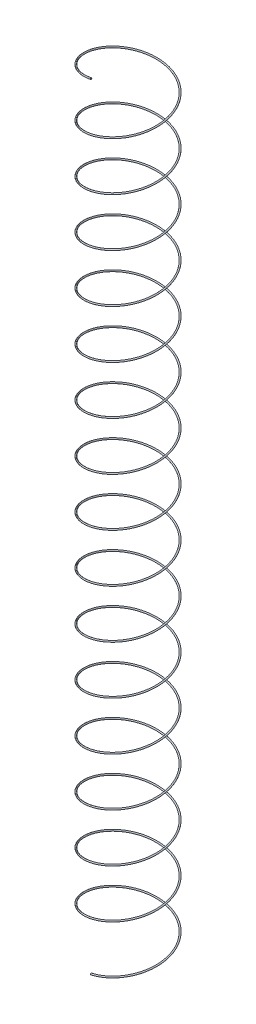
SolidWorks part; units mm, degrees
ref_plane "Front Plane" through (0, 0, 0) normal (0, 0, 1) x (1, 0, 0)
ref_plane "Top Plane" through (0, 0, 0) normal (0, 1, 0) x (1, 0, 0)
ref_plane "Right Plane" through (0, 0, 0) normal (1, 0, 0) x (0, 0, -1)
sketch "Center Axis" plane through (0, 0, 0) normal (1, 0, 0) x (0, 0, -1)
  line L0 (0, 0) -> (0, 49.506) construction
sketch "Diameter Stowed" plane through (0, 0, 0) normal (0, 1, 0) x (1, 0, 0)
  circle A0 centre (0, 0) radius 22.495
  dimension "D1" = 44.99
sketch "Diameter Deployed" plane through (0, 0, 0) normal (0, 1, 0) x (1, 0, 0)
  circle A0 centre (0, 0) radius 21.75
  dimension "D1" = 43.5
sketch "Wire Gauge XZ" plane through (0, 0, 0) normal (0, 1, 0) x (1, 0, 0)
  circle A0 centre (0, 0) radius 0.405
  dimension "D1" = 0.81
sketch "Wire Gauge YZ" plane through (0, 0, 0) normal (1, 0, 0) x (0, 0, -1)
  line L0 (0.405, 0) -> (-0.405, 0) construction
  line L1 (0, 0) -> (-0.405, 0) construction
  circle A0 centre (0, 0) radius 0.405
curve "Deployed Helix" pitch 28.6 height 457.6 turns 16
sketch "Sketch7" plane through (0, 0, 0) normal (1, 0, 0) x (0, 0, -1)
  circle A0 centre (-21.75, 0) radius 0.405
  circle A1 centre (0, 0) radius 0.405 construction
  spline S0 degree 3 poles (-21.75, 0) (-21.75, 0.4564) (-21.0842, 1.3749) (-18.1784, 2.7481) (-13.6284, 4.1226) (-7.8457, 5.4967) (-1.3533, 6.8709) (5.2614, 8.245) (11.4003, 9.6192) (16.508, 10.9934) (20.1226, 12.3676) (21.917, 13.7417) (21.7291, 15.1159) (19.5757, 16.4901) (15.6518, 17.8643) (10.3121, 19.2384) (4.0397, 20.6126) (-2.5982, 21.9868) (-9.001, 23.361) (-14.5896, 24.7351) (-18.8586, 26.1093) (-21.4219, 27.4835) (-22.0475, 28.8577) (-20.679, 30.2318) (-17.44, 31.606) (-12.6235, 32.9802) (-6.6653, 34.3544) (-0.1042, 35.7285) (6.4664, 37.1027) (12.452, 38.4769) (17.3114, 39.8511) (20.6049, 41.2252) (22.0348, 42.5994) (21.4715, 43.9736) (18.9662, 45.3477) (14.7454, 46.7219) (9.1908, 48.0961) (2.8049, 49.4703) (-3.8347, 50.8444) (-10.1274, 52.2186) (-15.5041, 53.5928) (-19.4784, 54.967) (-21.691, 56.3411) (-21.9415, 57.7153) (-20.2075, 59.0895) (-16.6457, 60.4637) (-11.5782, 61.8378) (-5.4635, 63.212) (1.1453, 64.5862) (7.6506, 65.9604) (13.4639, 67.3345) (18.0593, 68.7087) (21.0213, 70.0829) (22.0819, 71.4571) (21.1452, 72.8312) (18.2959, 74.2054) (13.7917, 75.5796) (8.0401, 76.9538) (1.5612, 78.3279) (-5.0589, 79.7021) (-11.2214, 81.0763) (-16.3689, 82.4505) (-20.0359, 83.8246) (-21.8906, 85.1988) (-21.7653, 86.573) (-19.6713, 87.9471) (-15.798, 89.3213) (-10.4958, 90.6955) (-4.2443, 92.0697) (2.3912, 93.4438) (8.8103, 94.818) (14.4326, 96.1922) (18.7494, 97.5664) (21.3704, 98.9405) (22.0583, 100.3147) (20.7511, 101.6889) (17.567, 103.0631) (12.7939, 104.4372) (6.8636, 105.8114) (0.3125, 107.1856) (-6.2669, 108.5598) (-12.2794, 109.9339) (-17.1813, 111.3081) (-20.5291, 112.6823) (-22.02, 114.0565) (-21.5193, 115.4306) (-19.0721, 116.8048) (-14.8998, 118.179) (-9.3798, 119.5532) (-3.0114, 120.9273) (3.6293, 122.3015) (9.9418, 123.6757) (15.3551, 125.0498) (19.3794, 126.424) (21.6509, 127.7982) (21.9641, 129.1724) (20.2906, 130.5465) (16.7818, 131.9207) (11.7551, 133.2949) (5.6652, 134.6691) (-0.9372, 136.0432) (-7.4548, 137.4174) (-13.2981, 138.7916) (-17.9386, 140.1658) (-20.9566, 141.5399) (-22.079, 142.9141) (-21.2043, 144.2883) (-18.4117, 145.6625) (-13.9538, 147.0366) (-8.2338, 148.4108) (-1.7689, 149.785) (4.8559, 151.1592) (11.0415, 152.5333) (16.2283, 153.9075) (19.9474, 155.2817) (21.8622, 156.6559) (21.7995, 158.03) (19.7651, 159.4042) (15.9429, 160.7784) (10.6787, 162.1526) (4.4485, 163.5267) (-2.1839, 164.9009) (-8.6189, 166.2751) (-14.2743, 167.6492) (-18.6385, 169.0234) (-21.3169, 170.3976) (-22.0672, 171.7718) (-20.8215, 173.1459) (-17.6925, 174.5201) (-12.9631, 175.8943) (-7.0613, 177.2685) (-0.5208, 178.6426) (6.0668, 180.0168) (12.1057, 181.391) (17.0496, 182.7652) (20.4514, 184.1393) (22.0033, 185.5135) (21.5651, 186.8877) (19.1762, 188.2619) (15.0529, 189.636) (9.568, 191.0102) (3.2177, 192.3844) (-3.4237, 193.7586) (-9.7553, 195.1327) (-15.2046, 196.5069) (-19.2787, 197.8811) (-21.609, 199.2553) (-21.9847, 200.6294) (-20.3719, 202.0036) (-16.9165, 203.3778) (-11.931, 204.752) (-5.8663, 206.1261) (0.729, 207.5003) (7.2584, 208.8745) (13.1312, 210.2486) (17.8163, 211.6228) (20.8899, 212.997) (22.0741, 214.3712) (21.2616, 215.7453) (18.526, 217.1195) (14.1147, 218.4937) (8.4267, 219.8679) (1.9765, 221.242) (-4.6524, 222.6162) (-10.8605, 223.9904) (-16.0863, 225.3646) (-19.8571, 226.7387) (-21.8318, 228.1129) (-21.8318, 229.4871) (-19.8571, 230.8613) (-16.0863, 232.2354) (-10.8605, 233.6096) (-4.6524, 234.9838) (1.9765, 236.358) (8.4267, 237.7321) (14.1147, 239.1063) (18.526, 240.4805) (21.2616, 241.8547) (22.0741, 243.2288) (20.8899, 244.603) (17.8163, 245.9772) (13.1312, 247.3514) (7.2584, 248.7255) (0.729, 250.0997) (-5.8663, 251.4739) (-11.931, 252.848) (-16.9165, 254.2222) (-20.3719, 255.5964) (-21.9847, 256.9706) (-21.609, 258.3447) (-19.2787, 259.7189) (-15.2046, 261.0931) (-9.7553, 262.4673) (-3.4237, 263.8414) (3.2177, 265.2156) (9.568, 266.5898) (15.0529, 267.964) (19.1762, 269.3381) (21.5651, 270.7123) (22.0033, 272.0865) (20.4514, 273.4607) (17.0496, 274.8348) (12.1057, 276.209) (6.0668, 277.5832) (-0.5208, 278.9574) (-7.0613, 280.3315) (-12.9631, 281.7057) (-17.6925, 283.0799) (-20.8215, 284.4541) (-22.0672, 285.8282) (-21.3169, 287.2024) (-18.6385, 288.5766) (-14.2743, 289.9508) (-8.6189, 291.3249) (-2.1839, 292.6991) (4.4485, 294.0733) (10.6787, 295.4474) (15.9429, 296.8216) (19.7651, 298.1958) (21.7995, 299.57) (21.8622, 300.9441) (19.9474, 302.3183) (16.2283, 303.6925) (11.0415, 305.0667) (4.8559, 306.4408) (-1.7689, 307.815) (-8.2338, 309.1892) (-13.9538, 310.5634) (-18.4117, 311.9375) (-21.2043, 313.3117) (-22.079, 314.6859) (-20.9566, 316.0601) (-17.9386, 317.4342) (-13.2981, 318.8084) (-7.4548, 320.1826) (-0.9372, 321.5568) (5.6652, 322.9309) (11.7551, 324.3051) (16.7818, 325.6793) (20.2906, 327.0535) (21.9641, 328.4276) (21.6509, 329.8018) (19.3794, 331.176) (15.3551, 332.5502) (9.9418, 333.9243) (3.6293, 335.2985) (-3.0114, 336.6727) (-9.3798, 338.0468) (-14.8998, 339.421) (-19.0721, 340.7952) (-21.5193, 342.1694) (-22.02, 343.5435) (-20.5291, 344.9177) (-17.1813, 346.2919) (-12.2794, 347.6661) (-6.2669, 349.0402) (0.3125, 350.4144) (6.8636, 351.7886) (12.7939, 353.1628) (17.567, 354.5369) (20.7511, 355.9111) (22.0583, 357.2853) (21.3704, 358.6595) (18.7494, 360.0336) (14.4326, 361.4078) (8.8103, 362.782) (2.3912, 364.1562) (-4.2443, 365.5303) (-10.4958, 366.9045) (-15.798, 368.2787) (-19.6713, 369.6529) (-21.7653, 371.027) (-21.8906, 372.4012) (-20.0359, 373.7754) (-16.3689, 375.1495) (-11.2214, 376.5237) (-5.0589, 377.8979) (1.5612, 379.2721) (8.0401, 380.6462) (13.7917, 382.0204) (18.2959, 383.3946) (21.1452, 384.7688) (22.0819, 386.1429) (21.0213, 387.5171) (18.0593, 388.8913) (13.4639, 390.2655) (7.6506, 391.6396) (1.1453, 393.0138) (-5.4635, 394.388) (-11.5782, 395.7622) (-16.6457, 397.1363) (-20.2075, 398.5105) (-21.9415, 399.8847) (-21.691, 401.2589) (-19.4784, 402.633) (-15.5041, 404.0072) (-10.1274, 405.3814) (-3.8347, 406.7556) (2.8049, 408.1297) (9.1908, 409.5039) (14.7454, 410.8781) (18.9662, 412.2523) (21.4715, 413.6264) (22.0348, 415.0006) (20.6049, 416.3748) (17.3114, 417.7489) (12.452, 419.1231) (6.4664, 420.4973) (-0.1042, 421.8715) (-6.6653, 423.2456) (-12.6235, 424.6198) (-17.44, 425.994) (-20.679, 427.3682) (-22.0475, 428.7423) (-21.4219, 430.1165) (-18.8586, 431.4907) (-14.5896, 432.8649) (-9.001, 434.239) (-2.5982, 435.6132) (4.0397, 436.9874) (10.3121, 438.3616) (15.6518, 439.7357) (19.5757, 441.1099) (21.7291, 442.4841) (21.917, 443.8583) (20.1226, 445.2324) (16.508, 446.6066) (11.4003, 447.9808) (5.2614, 449.355) (-1.3533, 450.7291) (-7.8457, 452.1033) (-13.6284, 453.4774) (-18.1784, 454.8519) (-21.0842, 456.2251) (-21.75, 457.1436) (-21.75, 457.6) knots 0 0 0 0 0.003003 0.006006 0.009009 0.012012 0.015015 0.018018 0.021021 0.024024 0.027027 0.03003 0.033033 0.036036 0.039039 0.042042 0.045045 0.048048 0.051051 0.054054 0.057057 0.06006 0.063063 0.066066 0.069069 0.072072 0.075075 0.078078 0.081081 0.084084 0.087087 0.09009 0.093093 0.096096 0.099099 0.102102 0.105105 0.108108 0.111111 0.114114 0.117117 0.12012 0.123123 0.126126 0.129129 0.132132 0.135135 0.138138 0.141141 0.144144 0.147147 0.15015 0.153153 0.156156 0.159159 0.162162 0.165165 0.168168 0.171171 0.174174 0.177177 0.18018 0.183183 0.186186 0.189189 0.192192 0.195195 0.198198 0.201201 0.204204 0.207207 0.21021 0.213213 0.216216 0.219219 0.222222 0.225225 0.228228 0.231231 0.234234 0.237237 0.24024 0.243243 0.246246 0.249249 0.252252 0.255255 0.258258 0.261261 0.264264 0.267267 0.27027 0.273273 0.276276 0.279279 0.282282 0.285285 0.288288 0.291291 0.294294 0.297297 0.3003 0.303303 0.306306 0.309309 0.312312 0.315315 0.318318 0.321321 0.324324 0.327327 0.33033 0.333333 0.336336 0.339339 0.342342 0.345345 0.348348 0.351351 0.354354 0.357357 0.36036 0.363363 0.366366 0.369369 0.372372 0.375375 0.378378 0.381381 0.384384 0.387387 0.39039 0.393393 0.396396 0.399399 0.402402 0.405405 0.408408 0.411411 0.414414 0.417417 0.42042 0.423423 0.426426 0.429429 0.432432 0.435435 0.438438 0.441441 0.444444 0.447447 0.45045 0.453453 0.456456 0.459459 0.462462 0.465465 0.468468 0.471471 0.474474 0.477477 0.48048 0.483483 0.486486 0.489489 0.492492 0.495495 0.498498 0.501502 0.504505 0.507508 0.510511 0.513514 0.516517 0.51952 0.522523 0.525526 0.528529 0.531532 0.534535 0.537538 0.540541 0.543544 0.546547 0.54955 0.552553 0.555556 0.558559 0.561562 0.564565 0.567568 0.570571 0.573574 0.576577 0.57958 0.582583 0.585586 0.588589 0.591592 0.594595 0.597598 0.600601 0.603604 0.606607 0.60961 0.612613 0.615616 0.618619 0.621622 0.624625 0.627628 0.630631 0.633634 0.636637 0.63964 0.642643 0.645646 0.648649 0.651652 0.654655 0.657658 0.660661 0.663664 0.666667 0.66967 0.672673 0.675676 0.678679 0.681682 0.684685 0.687688 0.690691 0.693694 0.696697 0.6997 0.702703 0.705706 0.708709 0.711712 0.714715 0.717718 0.720721 0.723724 0.726727 0.72973 0.732733 0.735736 0.738739 0.741742 0.744745 0.747748 0.750751 0.753754 0.756757 0.75976 0.762763 0.765766 0.768769 0.771772 0.774775 0.777778 0.780781 0.783784 0.786787 0.78979 0.792793 0.795796 0.798799 0.801802 0.804805 0.807808 0.810811 0.813814 0.816817 0.81982 0.822823 0.825826 0.828829 0.831832 0.834835 0.837838 0.840841 0.843844 0.846847 0.84985 0.852853 0.855856 0.858859 0.861862 0.864865 0.867868 0.870871 0.873874 0.876877 0.87988 0.882883 0.885886 0.888889 0.891892 0.894895 0.897898 0.900901 0.903904 0.906907 0.90991 0.912913 0.915916 0.918919 0.921922 0.924925 0.927928 0.930931 0.933934 0.936937 0.93994 0.942943 0.945946 0.948949 0.951952 0.954955 0.957958 0.960961 0.963964 0.966967 0.96997 0.972973 0.975976 0.978979 0.981982 0.984985 0.987988 0.990991 0.993994 0.996997 1 1 1 1 construction
sweep "Deployed" add profiles "Sketch7" path "Deployed Helix"
